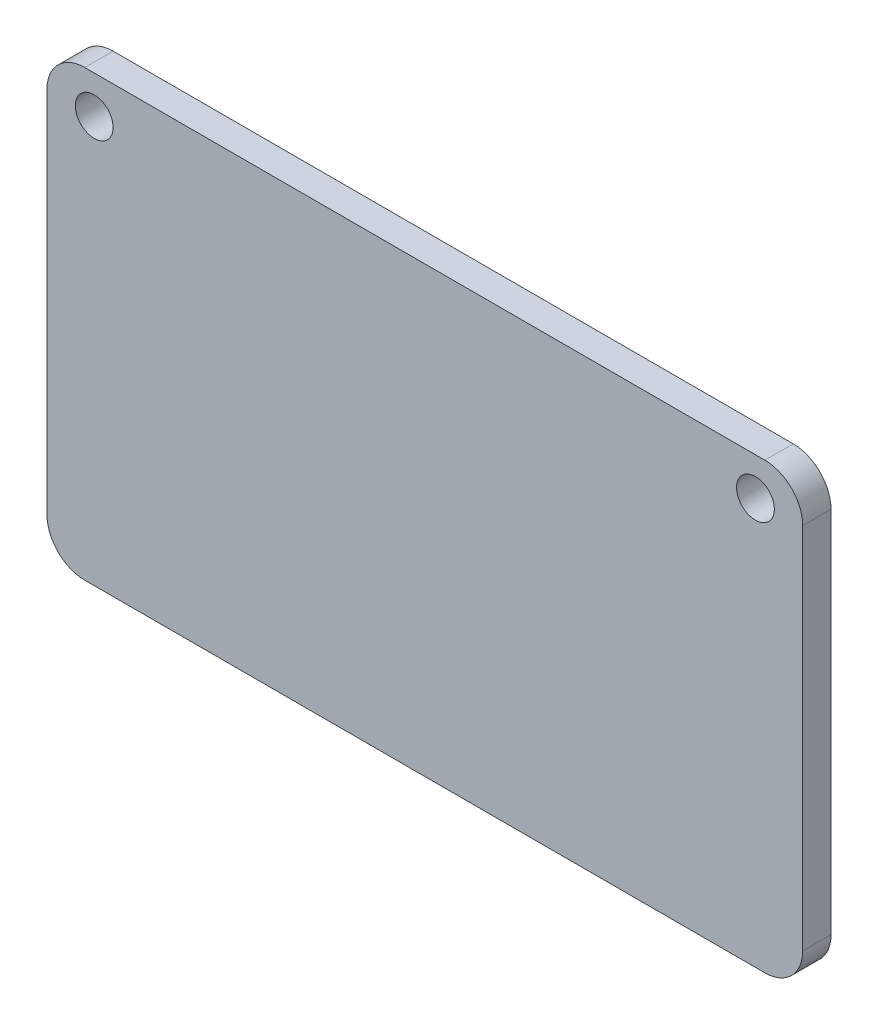
SolidWorks part; units mm, degrees
ref_plane "Plan de face" through (0, 0, 0) normal (0, 0, 1) x (1, 0, 0)
ref_plane "Plan de dessus" through (0, 0, 0) normal (0, 1, 0) x (1, 0, 0)
ref_plane "Plan de droite" through (0, 0, 0) normal (1, 0, 0) x (0, 0, -1)
sketch "Esquisse1" plane through (0, 0, 0) normal (0, 0, 1) x (1, 0, 0)
  line L0 (0, -4) -> (80, -4) construction
  line L1 (0, 0) -> (80, 0)
  line L2 (0, 0) -> (0, -47)
  line L3 (0, -47) -> (80, -47)
  line L4 (80, 0) -> (80, -47)
  line L5 (40, -4) -> (40, -47) construction
  circle A0 centre (5, -4) radius 2
  circle A1 centre (75, -4) radius 2
  dimension "D1" = 4
  dimension "D2" = 70
  dimension "D3" = 4
  dimension "D4" = 5
  dimension "D5" = 47
extrude "Boss.-Extru.1" add sketch "Esquisse1" along normal blind 3
fillet "Congé1" radius 4 4 edges at (80, -47, 1.5) (80, 0, 1.5) (0, -47, 1.5) (0, 0, 1.5)
